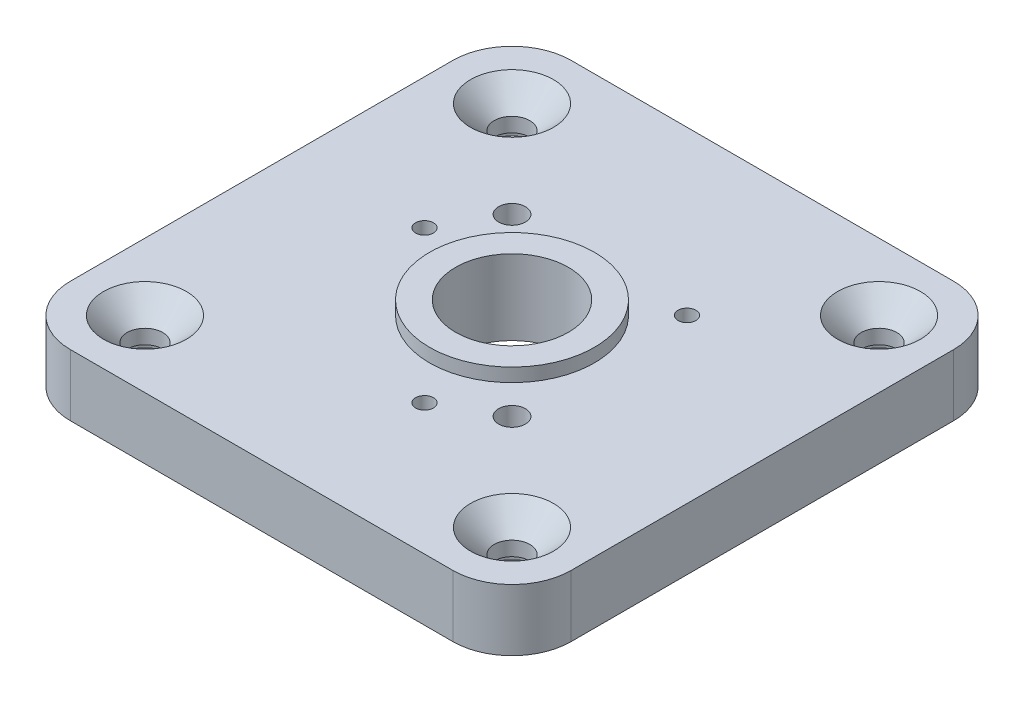
SolidWorks part; units mm, degrees
ref_plane "Front Plane" through (0, 0, 0) normal (0, 0, 1) x (1, 0, 0)
ref_plane "Top Plane" through (0, 0, 0) normal (0, 1, 0) x (1, 0, 0)
ref_plane "Right Plane" through (0, 0, 0) normal (1, 0, 0) x (0, 0, -1)
sketch "Sketch1" plane through (0, 0, 0) normal (0, 1, 0) x (1, 0, 0)
  line L0 (0, 42.3) -> (42.3, 0) construction
  line L1 (0, 0) -> (42.3, 0)
  line L2 (0, 0) -> (0, 42.3)
  line L3 (0, 42.3) -> (42.3, 42.3)
  line L4 (42.3, 0) -> (42.3, 42.3)
  line L6 (36.65, 36.65) -> (5.65, 36.65) construction
  line L7 (36.65, 36.65) -> (36.65, 5.65) construction
  line L8 (36.65, 5.65) -> (5.65, 5.65) construction
  line L9 (5.65, 36.65) -> (5.65, 5.65) construction
  line L10 (36.65, 36.65) -> (5.65, 5.65) construction
  line L11 (36.65, 5.65) -> (5.65, 36.65) construction
  circle A0 centre (36.65, 36.65) radius 1.5
  circle A1 centre (5.65, 5.65) radius 1.5
  circle A2 centre (36.65, 5.65) radius 1.5
  circle A3 centre (5.65, 36.65) radius 1.5
  circle A4 centre (21.15, 21.15) radius 4.7625
  point P5 (21.15, 21.15)
  dimension "D4" = 3
  dimension "D5" = 3
  dimension "D6" = 3
  dimension "D7" = 3
  dimension "D8" = 9.525
  dimension "D1" = 42.3
  dimension "D2" = 42.3
  dimension "D3" = 31
extrude "Boss-Extrude1" add sketch "Sketch1" along normal blind 5.21
sketch "Sketch2" plane through (0, 5.21, 0) normal (0, 1, 0) x (1, 0, 0)
  line L0 (21.15, 21.15) -> (42.3, 21.15) construction
  line L1 (42.3, 0) -> (42.3, 42.3) construction
  line L2 (21.15, 21.15) -> (28.5393, 28.5393) construction
  line L3 (5.65, 36.65) -> (36.65, 5.65) construction
  circle A0 centre (21.15, 21.15) radius 10.45 construction
  circle A1 centre (11.0561, 23.8547) radius 0.7557
  circle A2 centre (28.5393, 28.5393) radius 0.7556
  circle A3 centre (23.8547, 11.0561) radius 0.7556
  circle A4 centre (28.5393, 13.7607) radius 1.1303
  circle A5 centre (13.7607, 28.5393) radius 1.1303
  point P11 (21.15, 21.15)
  point P23 (21.15, 21.15)
  dimension "D1" = 1.5113
  dimension "D3" = 20.9
  dimension "D5" = 2.2606
  dimension "D4" = 45
  dimension "D2" = 3
  dimension "D6" = 2
extrude "Cut-Extrude1" cut sketch "Sketch2" against normal through all
chamfer "Chamfer1" distance 2 angle 45 4 edges at (5.65, 5.21, -4.15) (36.65, 5.21, -4.15) (36.65, 5.21, -35.15) (5.65, 5.21, -35.15)
sketch "Sketch3" [suppressed] plane through (0, 3.175, 0) normal (0, 1, 0) x (1, 0, 0)
  line L1 (21.175, 36.68) -> (21.125, 36.68)
  line L2 (36.675, 21.18) -> (36.675, -10.46)
  line L3 (36.675, -10.46) -> (5.625, -10.46)
  line L4 (5.625, 21.18) -> (5.625, -10.46)
  circle A0 centre (21.15, 21.15) radius 4.7625 construction
  circle A1 centre (21.15, 21.15) radius 4.7625 construction
  arc A2 (21.175, 36.68) -> (36.675, 21.18) centre (21.175, 21.18) cw
  arc A3 (21.125, 36.68) -> (5.625, 21.18) centre (21.125, 21.18) ccw
  point P9 (36.675, 36.68)
  dimension "D5" = 15.5
  dimension "D1" = 31.05
  dimension "D2" = 47.14
  dimension "D3" = 31.61
  dimension "D4" = 15.525
sketch "Sketch4" plane through (0, 5.21, 0) normal (0, 1, 0) x (1, 0, 0)
  circle A0 centre (21.15, 21.15) radius 4.7625 construction
  circle A1 centre (21.15, 21.15) radius 4.7625
  circle A2 centre (21.15, 21.15) radius 6.96
  dimension "D1" = 13.92
extrude "Boss-Extrude2" add sketch "Sketch4" along normal blind 1.14
sketch "Sketch5" plane through (0, 0, 0) normal (0, -1, 0) x (1, 0, 0)
  circle A0 centre (5.65, -5.65) radius 1.5 construction
  circle A1 centre (36.65, -5.65) radius 1.5 construction
  circle A2 centre (5.65, -36.65) radius 1.5 construction
  circle A3 centre (36.65, -36.65) radius 1.5 construction
  circle A4 centre (5.65, -5.65) radius 1.5
  circle A5 centre (36.65, -5.65) radius 1.5
  circle A6 centre (5.65, -36.65) radius 1.5
  circle A7 centre (36.65, -36.65) radius 1.5
  circle A8 centre (36.65, -36.65) radius 4
  circle A9 centre (21.15, -21.15) radius 4.7625 construction
  circle A10 centre (21.15, -21.15) radius 4.7625 construction
  circle A11 centre (5.65, -36.65) radius 4
  circle A12 centre (5.65, -5.65) radius 4
  circle A13 centre (36.65, -5.65) radius 4
  point P25 (21.15, -21.15)
  dimension "D1" = 8
  dimension "D2" = 4
extrude "Cut-Extrude2" cut sketch "Sketch5" against normal blind 2
fillet "Fillet1" radius 5 4 edges at (42.3, 2.605, 0) (0, 2.605, 0) (0, 2.605, -42.3) (42.3, 2.605, -42.3)
equation "\"D5@Sketch1\"=\"D4@Sketch1\""
equation "\"D6@Sketch1\"=\"D4@Sketch1\""
equation "\"D7@Sketch1\"=\"D4@Sketch1\""
equation "\"D8@Sketch1\"=.375in"
equation "\"D4@Sketch3\"=\"D1@Sketch3\"/2"
